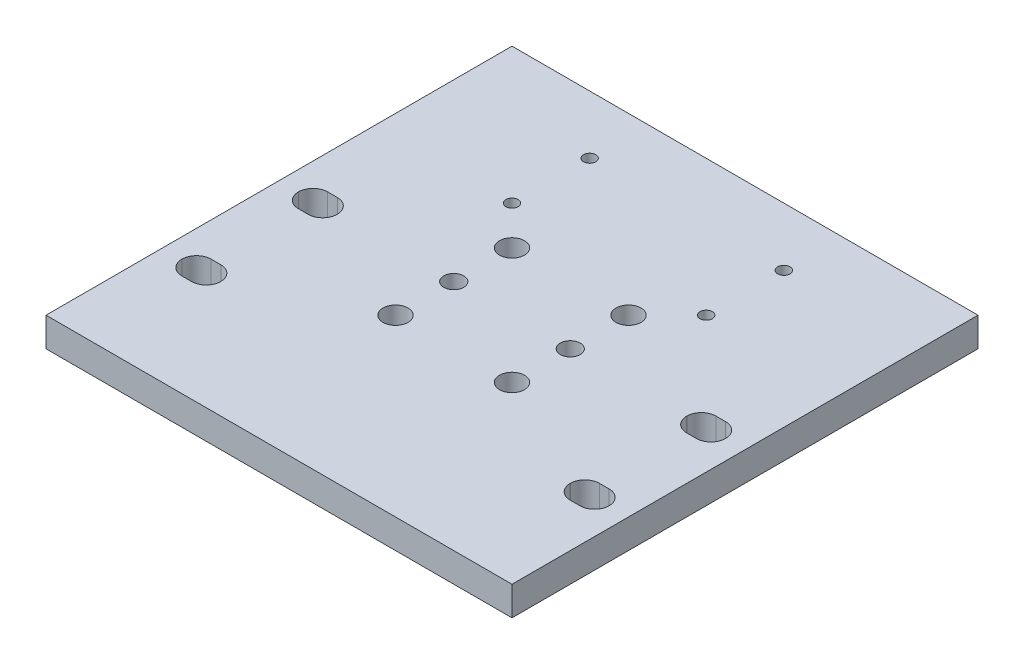
SolidWorks part; units mm, degrees
ref_plane "Front Plane" through (0, 0, 0) normal (0, 0, 1) x (1, 0, 0)
ref_plane "Top Plane" through (0, 0, 0) normal (0, 1, 0) x (1, 0, 0)
ref_plane "Right Plane" through (0, 0, 0) normal (1, 0, 0) x (0, 0, -1)
sketch "Sketch1" plane through (0, 0, 0) normal (0, 1, 0) x (1, 0, 0)
  line L1 (0, 0) -> (152.4, 0)
  line L2 (0, 0) -> (0, 152.4)
  line L3 (0, 152.4) -> (152.4, 152.4)
  line L4 (152.4, 0) -> (152.4, 152.4)
  dimension "D1" = 152.4
  dimension "D2" = 152.4
extrude "Extrude1" add sketch "Sketch1" along normal blind 9.525
sketch "Sketch2" plane through (0, 9.525, 0) normal (0, 1, 0) x (1, 0, 0)
  line L0 (76.2, 0) -> (76.2, 152.4) construction
  line L1 (0, 0) -> (152.4, 0) construction
  line L2 (152.4, 152.4) -> (0, 152.4) construction
  line L3 (139.7, 152.4) -> (139.7, 0) construction
  line L4 (12.7, 152.4) -> (12.7, 0) construction
  line L5 (152.4, 57.15) -> (0, 57.15) construction
  line L6 (141.2875, 33.3248) -> (138.1125, 33.3248)
  line L7 (146.05, 38.0873) -> (146.05, 38.1127)
  line L8 (19.05, 38.0873) -> (19.05, 38.1127)
  line L9 (11.1125, 80.9752) -> (14.2875, 80.9752)
  line L10 (6.35, 76.2127) -> (6.35, 76.1873)
  line L11 (11.1125, 71.4248) -> (14.2875, 71.4248)
  line L12 (19.05, 76.2127) -> (19.05, 76.1873)
  line L13 (11.1125, 42.8752) -> (14.2875, 42.8752)
  line L14 (6.35, 38.0873) -> (6.35, 38.1127)
  line L15 (11.1125, 33.3248) -> (14.2875, 33.3248)
  line L16 (141.2875, 42.8752) -> (138.1125, 42.8752)
  line L17 (133.35, 76.2127) -> (133.35, 76.1873)
  line L18 (141.2875, 71.4248) -> (138.1125, 71.4248)
  line L19 (146.05, 76.2127) -> (146.05, 76.1873)
  line L20 (141.2875, 80.9752) -> (138.1125, 80.9752)
  line L21 (133.35, 38.0873) -> (133.35, 38.1127)
  arc A0 (141.2875, 33.3248) -> (146.05, 38.0873) centre (141.2875, 38.0873) ccw
  arc A1 (133.35, 38.0873) -> (138.1125, 33.3248) centre (138.1125, 38.0873) ccw
  arc A2 (11.1125, 80.9752) -> (6.35, 76.2127) centre (11.1125, 76.2127) ccw
  arc A3 (19.05, 76.2127) -> (14.2875, 80.9752) centre (14.2875, 76.2127) ccw
  arc A4 (14.2875, 71.4248) -> (19.05, 76.1873) centre (14.2875, 76.1873) ccw
  arc A5 (6.35, 76.1873) -> (11.1125, 71.4248) centre (11.1125, 76.1873) ccw
  arc A6 (6.35, 38.1127) -> (11.1125, 42.8752) centre (11.1125, 38.1127) cw
  arc A7 (14.2875, 42.8752) -> (19.05, 38.1127) centre (14.2875, 38.1127) cw
  arc A8 (19.05, 38.0873) -> (14.2875, 33.3248) centre (14.2875, 38.0873) cw
  arc A9 (11.1125, 33.3248) -> (6.35, 38.0873) centre (11.1125, 38.0873) cw
  arc A10 (138.1125, 42.8752) -> (133.35, 38.1127) centre (138.1125, 38.1127) ccw
  arc A11 (146.05, 38.1127) -> (141.2875, 42.8752) centre (141.2875, 38.1127) ccw
  arc A12 (146.05, 76.1873) -> (141.2875, 71.4248) centre (141.2875, 76.1873) cw
  arc A13 (138.1125, 71.4248) -> (133.35, 76.1873) centre (138.1125, 76.1873) cw
  arc A14 (133.35, 76.2127) -> (138.1125, 80.9752) centre (138.1125, 76.2127) cw
  arc A15 (141.2875, 80.9752) -> (146.05, 76.2127) centre (141.2875, 76.2127) cw
  point P12 (76.2, 57.15)
  point P30 (19.05, 71.4248)
  point P33 (6.35, 71.4248)
  point P63 (146.05, 71.4248)
  point P64 (133.35, 71.4248)
  dimension "D6" = 4.7625
  dimension "D1" = 127
  dimension "D2" = 63.5
  dimension "D5" = 12.7
  dimension "D7" = 57.15
extrude "Cut-Extrude1" cut sketch "Sketch2" against normal through all
hole_wizard "#10-32 Tapped Hole1" positions "Sketch4" profile "Sketch3" tap size "#10-32" standard "Ansi Inch"
sketch "Sketch4" plane through (0, 9.525, 0) normal (0, 1, 0) x (-1, 0, 0)
  line L0 (-76.2, -152.4) -> (-76.2, 0) construction
  line L1 (-152.4, -152.4) -> (0, -152.4) construction
  line L2 (0, 0) -> (-152.4, 0) construction
  line L3 (0, -120.65) -> (-152.4, -120.65) construction
  point P0 (-44.45, -107.95)
  point P16 (-107.95, -107.95)
  point P18 (-107.95, -133.35)
  point P19 (-44.45, -133.35)
  dimension "D1" = 25.4
  dimension "D2" = 63.5
  dimension "D3" = 31.75
sketch "Sketch3" plane through (44.45, 9.525, -107.95) normal (1, 0, 0) x (0, 0, 1)
  line L0 (0, 0) -> (0, 14.8277)
  line L1 (0, 14.8277) -> (2.0193, 13.6144)
  line L2 (2.0193, 13.6144) -> (2.0193, 0)
  line L5 (2.0193, 0) -> (0, 0)
  line L10 (0, 14.8277) -> (-2.0193, 13.6144) construction
  line L11 (0, -6.35) -> (0, 107.95) construction
  dimension "Tap Drill Dia." = 4.0386
  dimension "Tap Drill Depth" = 13.6144
  dimension "Drill Angle" = 118
cosmetic thread "Hole Thread1" parameters "D1"=9.525, "D2"=4.826
cosmetic thread "Hole Thread2" parameters "D1"=9.525, "D2"=4.826
cosmetic thread "Hole Thread3" parameters "D1"=9.525, "D2"=4.826
cosmetic thread "Hole Thread4" parameters "D1"=9.525, "D2"=4.826
sketch "Sketch5" plane through (0, 9.525, 0) normal (0, 1, 0) x (1, 0, 0)
  line L0 (76.2, 152.4) -> (76.2, 0) construction
  line L1 (152.4, 152.4) -> (0, 152.4) construction
  line L2 (0, 0) -> (152.4, 0) construction
  line L3 (0, 76.2) -> (152.4, 76.2) construction
  line L4 (0, 152.4) -> (0, 0) construction
  line L5 (152.4, 0) -> (152.4, 152.4) construction
  circle A0 centre (57.15, 95.25) radius 4.0958
  circle A1 centre (95.25, 95.25) radius 4.0957
  circle A2 centre (57.15, 57.15) radius 4.0958
  circle A3 centre (95.25, 57.15) radius 4.0957
  dimension "D3" = 8.1915
  dimension "D1" = 38.1
  dimension "D2" = 38.1
extrude "Cut-Extrude2" cut sketch "Sketch5" against normal through all
hole_wizard "5/16-18 Tapped Hole1" positions "Sketch7" profile "Sketch6" tap size "5/16-18" standard "Ansi Inch"
sketch "Sketch7" plane through (0, 9.525, 0) normal (0, 1, 0) x (-1, 0, 0)
  line L0 (-76.2, -152.4) -> (-76.2, 0) construction
  line L1 (-152.4, -152.4) -> (0, -152.4) construction
  line L2 (0, 0) -> (-152.4, 0) construction
  line L3 (0, -76.2) -> (-152.4, -76.2) construction
  line L4 (0, -152.4) -> (0, 0) construction
  line L5 (-152.4, 0) -> (-152.4, -152.4) construction
  point P0 (-57.15, -76.2)
  point P10 (-95.25, -76.2)
  dimension "D1" = 38.1
sketch "Sketch6" plane through (57.15, 9.525, -76.2) normal (1, 0, 0) x (0, 0, 1)
  line L0 (0, 0) -> (0, 24.8973)
  line L1 (0, 24.8973) -> (3.2639, 22.9362)
  line L2 (3.2639, 22.9362) -> (3.2639, 0)
  line L5 (3.2639, 0) -> (0, 0)
  line L10 (0, 24.8973) -> (-3.2639, 22.9362) construction
  line L11 (0, -6.35) -> (0, 107.95) construction
  dimension "Tap Drill Dia." = 6.5278
  dimension "Tap Drill Depth" = 22.9362
  dimension "Drill Angle" = 118
cosmetic thread "Hole Thread5" parameters "D1"=9.525, "D2"=7.9375
cosmetic thread "Hole Thread6" parameters "D1"=9.525, "D2"=7.9375
